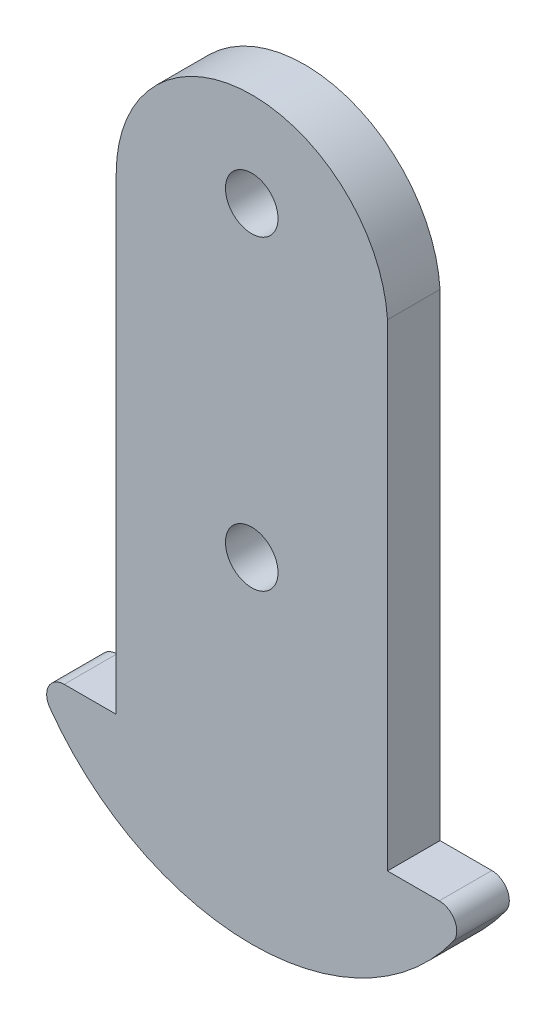
SolidWorks part; units mm, degrees
ref_plane "Front Plane" through (0, 0, 0) normal (0, 0, 1) x (1, 0, 0)
ref_plane "Top Plane" through (0, 0, 0) normal (0, 1, 0) x (1, 0, 0)
ref_plane "Right Plane" through (0, 0, 0) normal (1, 0, 0) x (0, 0, -1)
sketch "Sketch1" plane through (0, 0, 0) normal (0, 0, 1) x (1, 0, 0)
  line L0 (0, 16.5) -> (0, -16.5) construction
  line L5 (7.7414, 16.8914) -> (-7.7339, -16.875) construction
  line L6 (7.75, -16.375) -> (-7.75, 16.375) construction
  line L9 (-10.7044, -18) -> (10.7044, -18)
  line L10 (7.75, 9.25) -> (7.75, -18)
  line L11 (-7.7339, 8.75) -> (-7.7339, -18)
  circle A0 centre (0, 11.125) radius 1.5
  circle A1 centre (0, -6.375) radius 1.5
  arc A2 (-11.5173, -19.5823) -> (11.5173, -19.5823) centre (0, -11.3333) ccw
  arc A3 (-10.7044, -18) -> (-11.5173, -19.5823) centre (-10.7044, -19) ccw
  arc A4 (10.7044, -18) -> (11.5173, -19.5823) centre (10.7044, -19) cw
  arc A5 (7.75, 9.25) -> (-7.7339, 8.75) centre (0.0161, 8.75) ccw
  point P0 (0, 0)
  point P9 (0, 0)
  point P16 (3.875, -16.375)
  point P17 (0, -25.5)
  point P20 (-12.5, -16.375)
  point P23 (12.5, -16.375)
  dimension "D3" = 3
  dimension "D4" = 3
  dimension "D7" = 7.5
  dimension "D9" = 1
  dimension "D1" = 33
  dimension "D2" = 15.5
  dimension "D5" = 17.5
  dimension "D6" = 10
  dimension "D8" = 25
  dimension "D10" = 42
extrude "Boss-Extrude2" add sketch "Sketch1" along normal blind 3 contours L10 A5 L11 L9 A0 A1 | A4 L9 A3 A2
